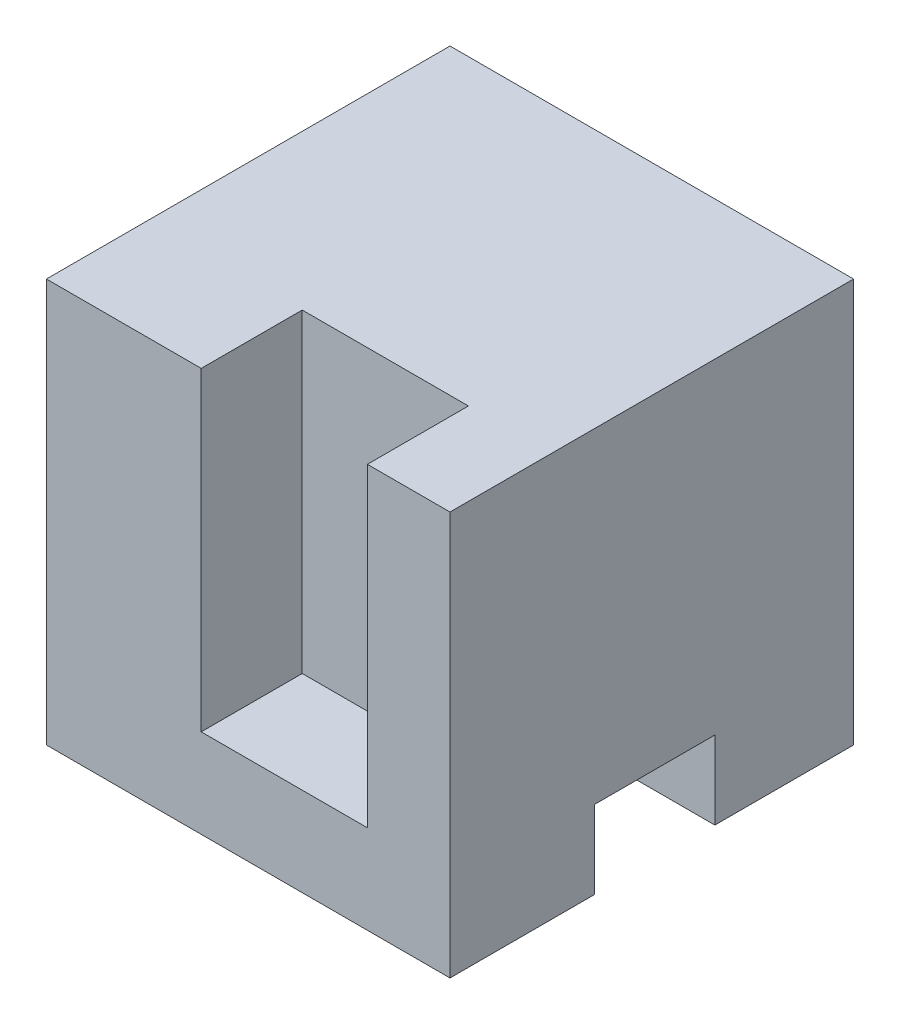
SolidWorks part; units mm, degrees
ref_plane "Přední rovina" through (0, 0, 0) normal (0, 0, 1) x (1, 0, 0)
ref_plane "Horní rovina" through (0, 0, 0) normal (0, 1, 0) x (1, 0, 0)
ref_plane "Pravá rovina" through (0, 0, 0) normal (1, 0, 0) x (0, 0, -1)
sketch "Skica2" plane through (0, 0, 0) normal (0, 0, 1) x (1, 0, 0)
  line L1 (0, 0) -> (50, 0)
  line L2 (0, 0) -> (0, 50)
  line L3 (0, 50) -> (50, 50)
  line L4 (50, 0) -> (50, 50)
  dimension "D1" = 50
  dimension "D2" = 50
extrude "Přidat vysunutím1" add sketch "Skica2" along normal mid plane 50
sketch "Skica3" plane through (0, 50, 0) normal (0, 1, 0) x (1, 0, 0)
  line L0 (50, -25) -> (0, -25) construction
  line L1 (19.1758, -25) -> (39.7643, -25)
  line L2 (19.1758, -25) -> (19.1758, -12.4823)
  line L3 (19.1758, -12.4823) -> (39.7643, -12.4823)
  line L4 (39.7643, -25) -> (39.7643, -12.4823)
extrude "Odebrat vysunutím1" cut sketch "Skica3" against normal blind 39
sketch "Skica4" plane through (50, 0, 0) normal (1, 0, 0) x (0, 0, -1)
  line L0 (-25, 0) -> (25, 0) construction
  line L1 (-7.0713, 0) -> (7.8136, 0)
  line L2 (-7.0713, 0) -> (-7.0713, 9.6676)
  line L3 (-7.0713, 9.6676) -> (7.8136, 9.6676)
  line L4 (7.8136, 0) -> (7.8136, 9.6676)
extrude "Odebrat vysunutím2" cut sketch "Skica4" against normal blind 39
sketch "Skica5" plane through (0, 0, 0) normal (-1, 0, 0) x (0, 0, 1)
  line L0 (-25, 50) -> (-25, 0) construction
  line L1 (-25, 43.5357) -> (-8.5731, 43.5357)
  line L2 (-25, 43.5357) -> (-25, 25)
  line L3 (-25, 25) -> (-8.5731, 25)
  line L4 (-8.5731, 43.5357) -> (-8.5731, 25)
extrude "Odebrat vysunutím3" cut sketch "Skica5" against normal blind 39
fillet "Zaoblit1" [suppressed] radius 10
hole_wizard "Kuželové zahloubení pro M6 šroubu se zápustnou hlavou plochou1" positions "Skica6" profile "Skica8" countersink size "M6" standard "ISO"
sketch "Skica6" plane through (0, 50, 0) normal (0, 1, 0) x (1, 0, 0)
  point P0 (29.2623, 3.8366)
sketch "Skica8" plane through (29.2623, 50, -3.8366) normal (1, 0, 0) x (0, 0, 1)
  line L0 (0, 0) -> (0, 50)
  line L1 (0, 50) -> (3.3, 50)
  line L2 (3.3, 50) -> (3.3, 3)
  line L3 (3.3, 3) -> (6.3, 0)
  line L5 (6.3, 0) -> (0, 0)
  line L6 (-3.3, 3) -> (-6.3, 0) construction
  line L11 (0, -6.35) -> (0, 107.95) construction
  dimension "Průměr díry skrz" = 6.6
  dimension "Hloubka díry skrz" = 50
  dimension "Průměr blíz. kuž. zahloubení" = 12.6
  dimension "Úhel blíz. kuž. zahloubení" = 90
equation "\"erere\"= \"SW-Objem\""
